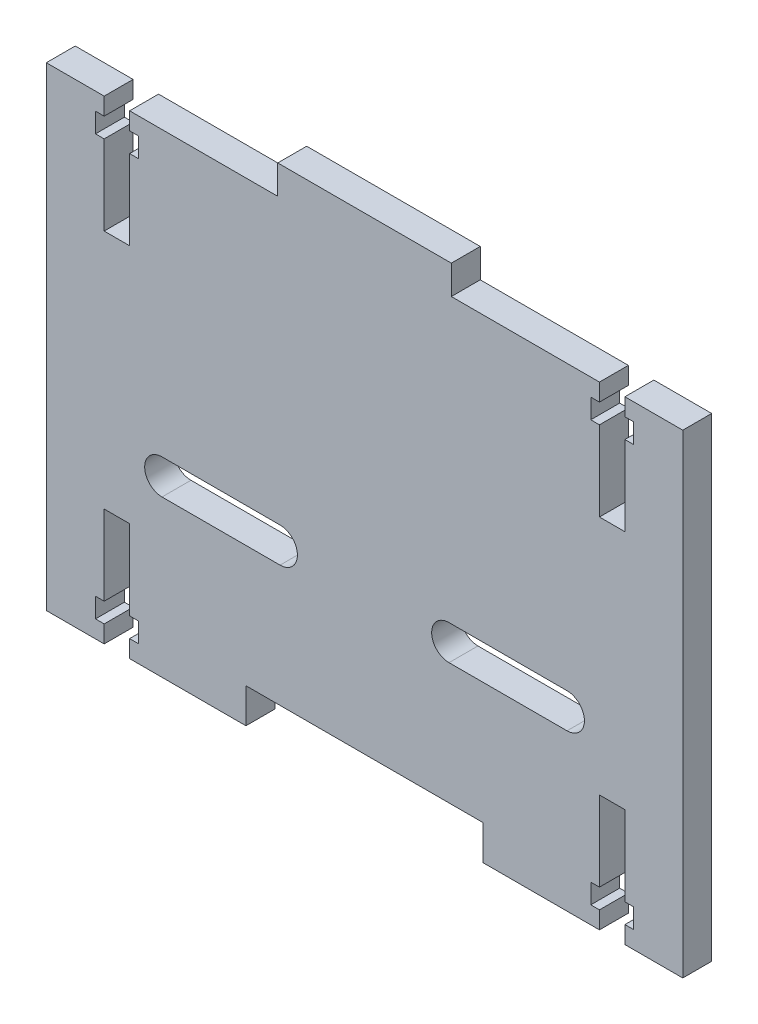
SolidWorks part; units mm, degrees
ref_plane "Front Plane" through (0, 0, 0) normal (0, 0, 1) x (1, 0, 0)
ref_plane "Top Plane" through (0, 0, 0) normal (0, 1, 0) x (1, 0, 0)
ref_plane "Right Plane" through (0, 0, 0) normal (1, 0, 0) x (0, 0, -1)
sketch "Sketch1" plane through (0, 0, 0) normal (0, 0, 1) x (1, 0, 0)
  line L0 (20.5, -41) -> (20.5, -35)
  line L1 (-55, 41) -> (-15, 41)
  line L2 (-55, 41) -> (-55, -41)
  line L3 (-55, -41) -> (-20.5, -41)
  line L4 (55, 41) -> (55, -41)
  line L5 (20.5, -35) -> (-20.5, -35)
  line L6 (-20.5, -35) -> (-20.5, -41)
  line L7 (20.5, -41) -> (55, -41)
  line L8 (15, 41) -> (15, 46)
  line L9 (15, 46) -> (-15, 46)
  line L10 (-15, 46) -> (-15, 41)
  line L11 (15, 41) -> (55, 41)
  dimension "D1" = 110
  dimension "D2" = 55
  dimension "D3" = 82
  dimension "D4" = 41
  dimension "D5" = 34.5
  dimension "D6" = 34.5
  dimension "D7" = 6
  dimension "D8" = 30
  dimension "D9" = 40
  dimension "D10" = 5
extrude "Boss-Extrude1" add sketch "Sketch1" along normal blind 5
sketch "Sketch2" plane through (0, 0, 0) normal (0, 0, -1) x (-1, 0, 0)
  line L0 (-42.8, -41) -> (-42.8, -26.1548) construction
  line L1 (-40.6, -38) -> (-40.6, -41)
  line L2 (-45, -34.6) -> (-45, -20.8)
  line L3 (-39.1, -34.6) -> (-40.6, -34.6)
  line L4 (-39.1, -38) -> (-39.1, -34.6)
  line L5 (-40.6, -38) -> (-39.1, -38)
  line L6 (-46.5, -34.6) -> (-45, -34.6)
  line L7 (-46.5, -38) -> (-46.5, -34.6)
  line L8 (-45, -38) -> (-46.5, -38)
  line L9 (-45, -41) -> (-40.6, -41)
  line L10 (-40.6, -20.8) -> (-40.6, -34.6)
  line L11 (-45, -20.8) -> (-40.6, -20.8)
  line L12 (-45, -41) -> (-45, -38)
  line L13 (-20.5, -41) -> (-55, -41) construction
  line L14 (-55, -41) -> (-55, 41) construction
  line L15 (0, 0) -> (0, -39.3618) construction
  line L16 (42.8, -41) -> (42.8, -26.1548) construction
  line L17 (45, -41) -> (45, -38)
  line L18 (45, -20.8) -> (40.6, -20.8)
  line L19 (40.6, -20.8) -> (40.6, -34.6)
  line L20 (45, -41) -> (40.6, -41)
  line L21 (45, -38) -> (46.5, -38)
  line L22 (46.5, -38) -> (46.5, -34.6)
  line L23 (46.5, -34.6) -> (45, -34.6)
  line L24 (40.6, -38) -> (39.1, -38)
  line L25 (39.1, -38) -> (39.1, -34.6)
  line L26 (39.1, -34.6) -> (40.6, -34.6)
  line L27 (45, -34.6) -> (45, -20.8)
  line L28 (40.6, -38) -> (40.6, -41)
  line L29 (0, 0) -> (24.2878, 0) construction
  line L30 (42.8, 41) -> (42.8, 26.1548) construction
  line L31 (40.6, 38) -> (40.6, 41)
  line L32 (45, 34.6) -> (45, 20.8)
  line L33 (39.1, 34.6) -> (40.6, 34.6)
  line L34 (39.1, 38) -> (39.1, 34.6)
  line L35 (40.6, 38) -> (39.1, 38)
  line L36 (46.5, 34.6) -> (45, 34.6)
  line L37 (46.5, 38) -> (46.5, 34.6)
  line L38 (45, 38) -> (46.5, 38)
  line L39 (45, 41) -> (40.6, 41)
  line L40 (40.6, 20.8) -> (40.6, 34.6)
  line L41 (45, 20.8) -> (40.6, 20.8)
  line L42 (45, 41) -> (45, 38)
  line L43 (-42.8, 41) -> (-42.8, 26.1548) construction
  line L44 (-45, 41) -> (-45, 38)
  line L45 (-45, 20.8) -> (-40.6, 20.8)
  line L46 (-40.6, 20.8) -> (-40.6, 34.6)
  line L47 (-45, 41) -> (-40.6, 41)
  line L48 (-45, 38) -> (-46.5, 38)
  line L49 (-46.5, 38) -> (-46.5, 34.6)
  line L50 (-46.5, 34.6) -> (-45, 34.6)
  line L51 (-40.6, 38) -> (-39.1, 38)
  line L52 (-39.1, 38) -> (-39.1, 34.6)
  line L53 (-39.1, 34.6) -> (-40.6, 34.6)
  line L54 (-45, 34.6) -> (-45, 20.8)
  line L55 (-40.6, 38) -> (-40.6, 41)
  dimension "D1" = 13.8
  dimension "D2" = 3.4
  dimension "D3" = 3
  dimension "D4" = 2.2
  dimension "D5" = 4.4
  dimension "D6" = 1.5
  dimension "D7" = 1.5
  dimension "D8" = 10
extrude "Cut-Extrude1" cut sketch "Sketch2" against normal blind 5
sketch "Sketch3" plane through (0, 0, 0) normal (0, 0, -1) x (-1, 0, 0)
  line L0 (-14.6, -11) -> (-35, -11) construction
  line L1 (-14.6, -14.1) -> (-14.6, -7.9) construction
  line L2 (-35, -1) -> (-35, -21) construction
  line L3 (-14.6, -14) -> (-35, -14)
  line L4 (-14.6, -8) -> (-35, -8)
  line L5 (0, 0) -> (0, -24.0608) construction
  line L6 (14.6, -11) -> (35, -11) construction
  line L7 (14.6, -14) -> (35, -14)
  line L8 (14.6, -8) -> (35, -8)
  arc A0 (-14.6, -14) -> (-14.6, -8) centre (-14.6, -11) ccw
  arc A1 (-35, -8) -> (-35, -14) centre (-35, -11) ccw
  arc A2 (14.6, -14) -> (14.6, -8) centre (14.6, -11) cw
  arc A3 (35, -8) -> (35, -14) centre (35, -11) cw
  point P6 (-24.8, -11)
  point P17 (24.8, -11)
  dimension "D1" = 6
extrude "Cut-Extrude2" cut sketch "Sketch3" against normal blind 10
